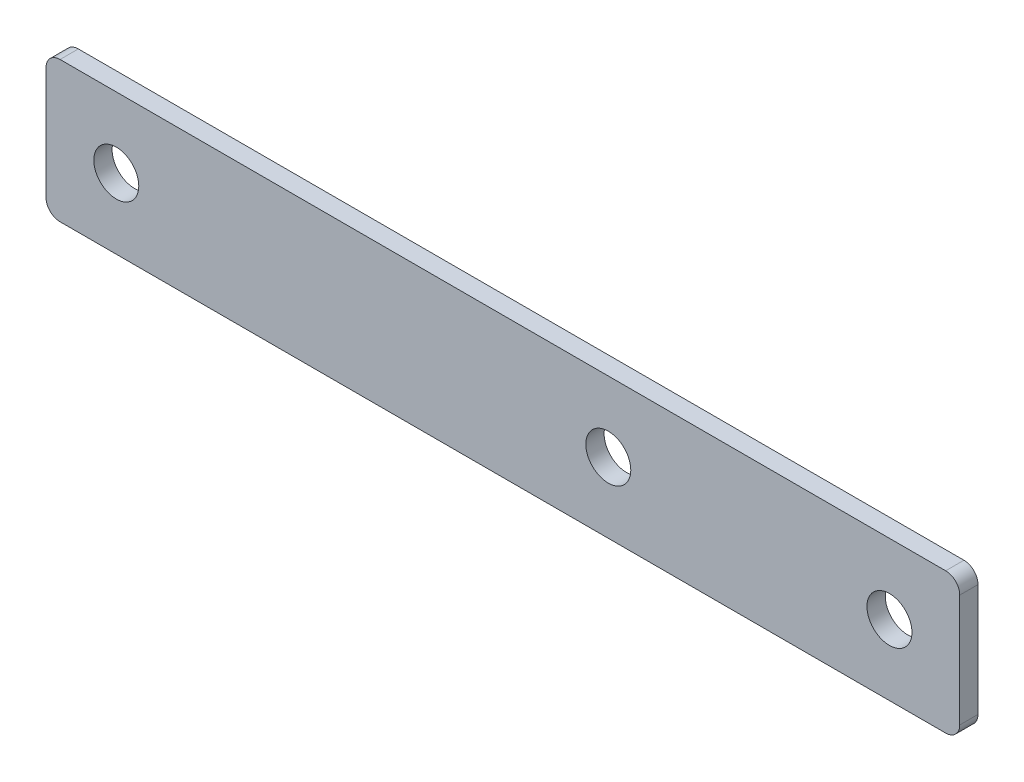
SolidWorks part; units mm, degrees
material "ABS"
ref_plane "前视基准面" through (0, 0, 0) normal (0, 0, 1) x (1, 0, 0)
ref_plane "上视基准面" through (0, 0, 0) normal (0, 1, 0) x (1, 0, 0)
ref_plane "右视基准面" through (0, 0, 0) normal (1, 0, 0) x (0, 0, -1)
sketch "草图1" plane through (0, 0, 0) normal (0, 0, 1) x (1, 0, 0)
  line L0 (0, 5) -> (65, 5) construction
  line L1 (0, 10) -> (65, 10)
  line L2 (0, 10) -> (0, 0)
  line L3 (0, 0) -> (65, 0)
  line L4 (65, 10) -> (65, 0)
  circle A0 centre (60, 5) radius 1.6
  circle A1 centre (40, 5) radius 1.6
  circle A2 centre (5, 5) radius 1.6
  dimension "D3" = 3.2
  dimension "D5" = 20
  dimension "D6" = 35
  dimension "D1" = 10
  dimension "D2" = 65
  dimension "D4" = 5
extrude "凸台-拉伸1" add sketch "草图1" along normal blind 1.3 contours L1 L4 L3 L2
fillet "圆角1" radius 1 4 edges at (65, 0, 0.65) (65, 10, 0.65) (0, 0, 0.65) (0, 10, 0.65)
